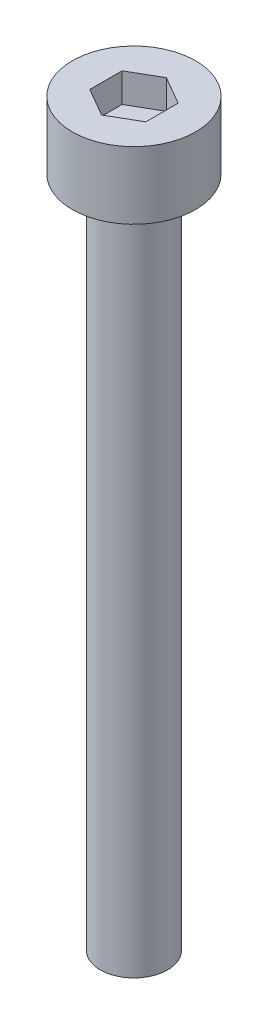
SolidWorks part; units mm, degrees
material "AISI Type A2 Tool Steel"
ref_plane "Front" through (0, 0, 0) normal (0, 0, 1) x (1, 0, 0)
ref_plane "Top" through (0, 0, 0) normal (0, 1, 0) x (1, 0, 0)
ref_plane "Right" through (0, 0, 0) normal (1, 0, 0) x (0, 0, -1)
sketch "Sketch1" plane through (0, 0, 0) normal (0, 1, 0) x (1, 0, 0)
  circle A0 centre (0, 0) radius 2.75
  dimension "D1" = 5.5
extrude "Boss-Extrude1" add sketch "Sketch1" along normal blind 3
sketch "Sketch2" plane through (0, 3, 0) normal (0, 1, 0) x (1, 0, 0)
  line L1 (0, 1.4434) -> (-1.25, 0.7217)
  line L2 (-1.25, 0.7217) -> (-1.25, -0.7217)
  line L3 (-1.25, -0.7217) -> (0, -1.4434)
  line L4 (0, -1.4434) -> (1.25, -0.7217)
  line L5 (1.25, -0.7217) -> (1.25, 0.7217)
  line L6 (1.25, 0.7217) -> (0, 1.4434)
  circle A0 centre (0, 0) radius 1.25 construction
  dimension "D1" = 2.5
extrude "Cut-Extrude1" cut sketch "Sketch2" against normal blind 1.3
sketch "Sketch3" plane through (0, 0, 0) normal (0, -1, 0) x (1, 0, 0)
  circle A0 centre (0, 0) radius 1.5
  dimension "D1" = 3
extrude "Boss-Extrude2" add sketch "Sketch3" along normal blind 30
equation "\"`2.40\"=2.8"
